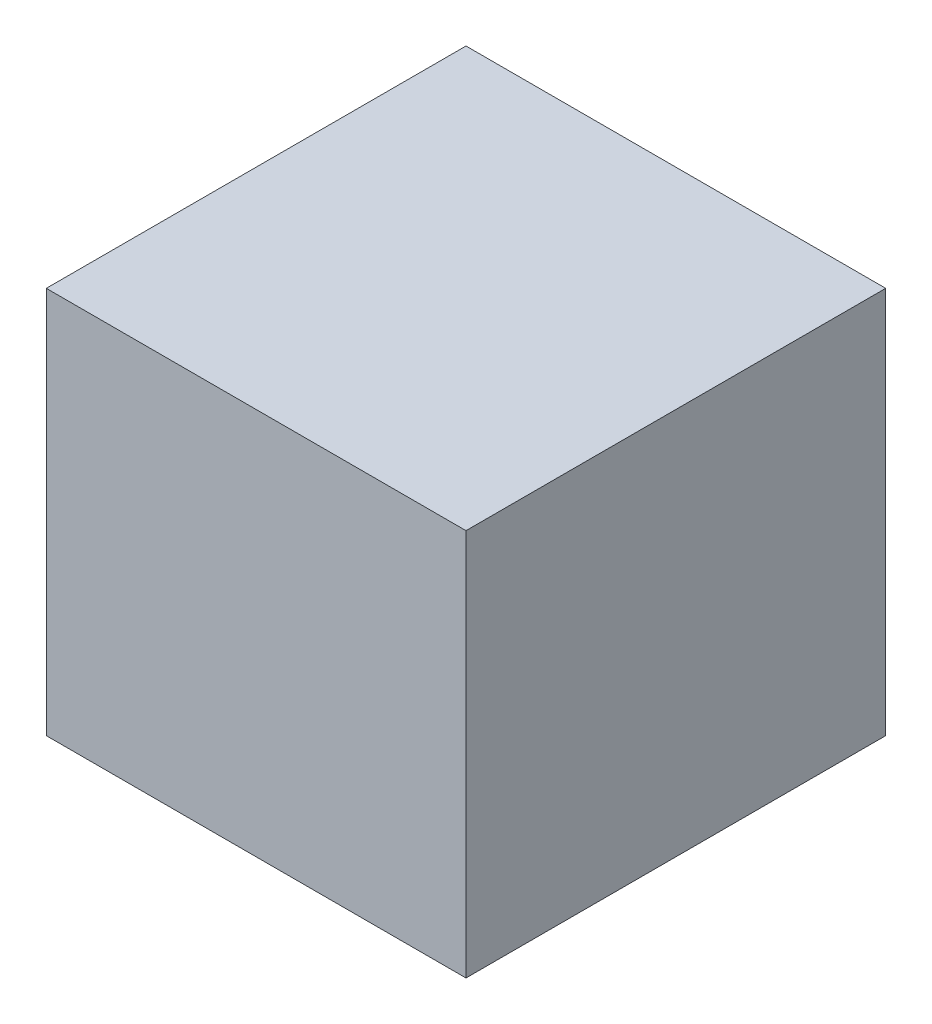
SolidWorks part; units mm, degrees
ref_plane "前视基准面" through (0, 0, 0) normal (0, 0, 1) x (1, 0, 0)
ref_plane "上视基准面" through (0, 0, 0) normal (0, 1, 0) x (1, 0, 0)
ref_plane "右视基准面" through (0, 0, 0) normal (1, 0, 0) x (0, 0, -1)
sketch "草图1" plane through (0, 0, 0) normal (0, 1, 0) x (1, 0, 0)
  line L1 (-16.25, 16.25) -> (16.25, 16.25)
  line L2 (-16.25, 16.25) -> (-16.25, -16.25)
  line L3 (-16.25, -16.25) -> (16.25, -16.25)
  line L4 (16.25, 16.25) -> (16.25, -16.25)
  line L5 (-16.25, 16.25) -> (16.25, -16.25) construction
  line L6 (-16.25, -16.25) -> (16.25, 16.25) construction
  point P0 (0, 0)
  dimension "D1" = 32.5
  dimension "D2" = 32.5
extrude "凸台-拉伸1" add sketch "草图1" along normal blind 30
